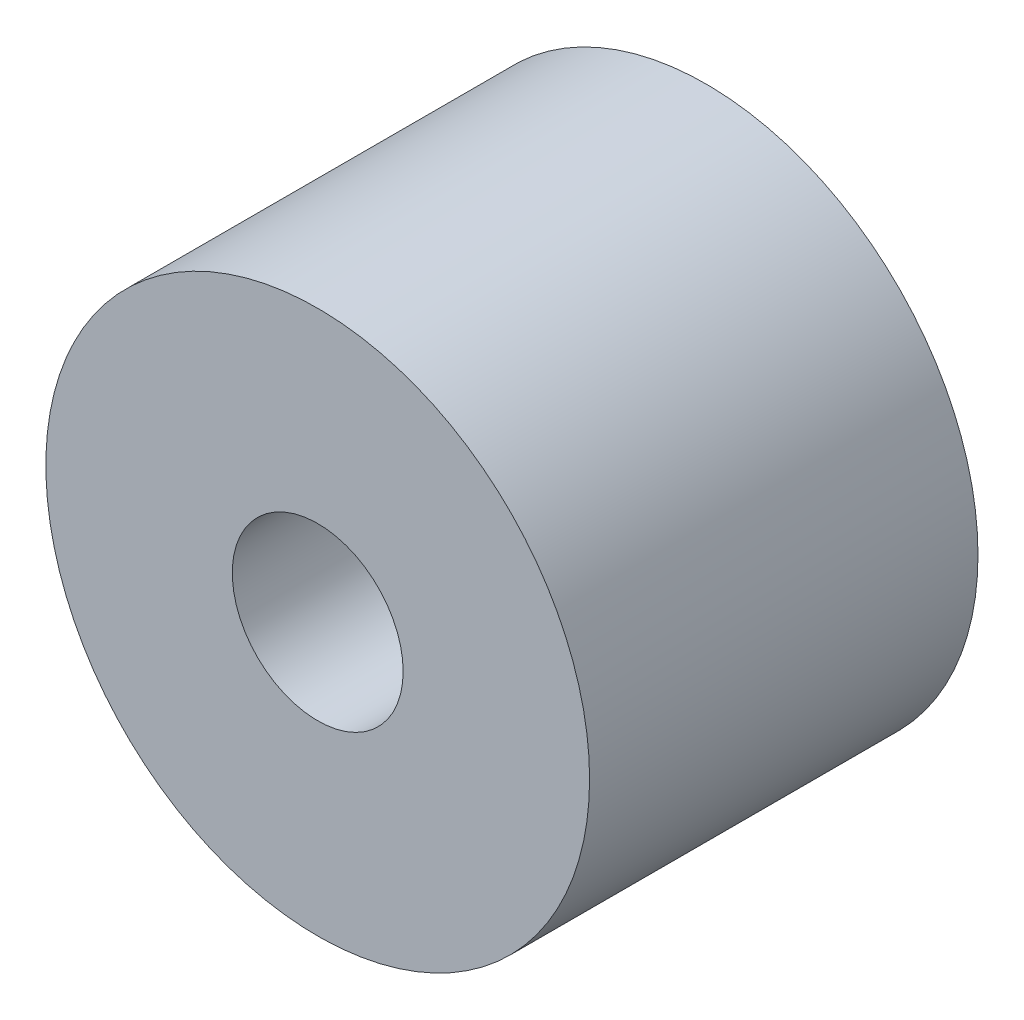
SolidWorks part; units mm, degrees
ref_plane "Plan de face" through (0, 0, 0) normal (0, 0, 1) x (1, 0, 0)
ref_plane "Plan de dessus" through (0, 0, 0) normal (0, 1, 0) x (1, 0, 0)
ref_plane "Plan de droite" through (0, 0, 0) normal (1, 0, 0) x (0, 0, -1)
sketch "Esquisse1" plane through (0, 0, 0) normal (0, 0, 1) x (1, 0, 0)
  circle A0 centre (0, 0) radius 1.1
  circle A1 centre (0, 0) radius 3.5
  dimension "D1" = 7
  dimension "D2" = 2.2
extrude "Boss.-Extru.1" add sketch "Esquisse1" along normal blind 5
